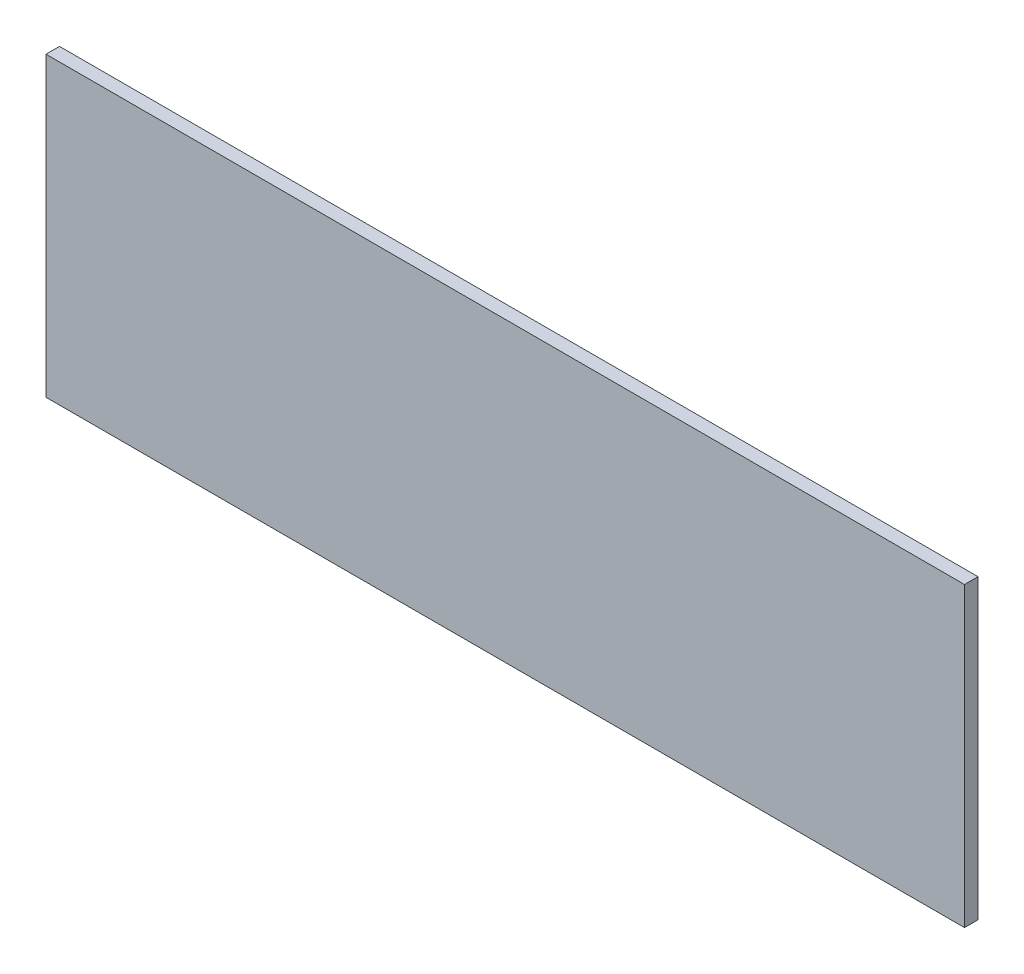
SolidWorks part; units mm, degrees
ref_plane "Front Plane" through (0, 0, 0) normal (0, 0, 1) x (1, 0, 0)
ref_plane "Top Plane" through (0, 0, 0) normal (0, 1, 0) x (1, 0, 0)
ref_plane "Right Plane" through (0, 0, 0) normal (1, 0, 0) x (0, 0, -1)
sketch "Sketch1" plane through (0, 0, 0) normal (0, 0, 1) x (1, 0, 0)
  line L1 (0, 0) -> (431.8, 0)
  line L2 (0, 0) -> (0, 139.7)
  line L3 (0, 139.7) -> (431.8, 139.7)
  line L4 (431.8, 0) -> (431.8, 139.7)
  dimension "D1" = 431.8
  dimension "D2" = 139.7
extrude "Boss-Extrude1" add sketch "Sketch1" along normal blind 6.35
